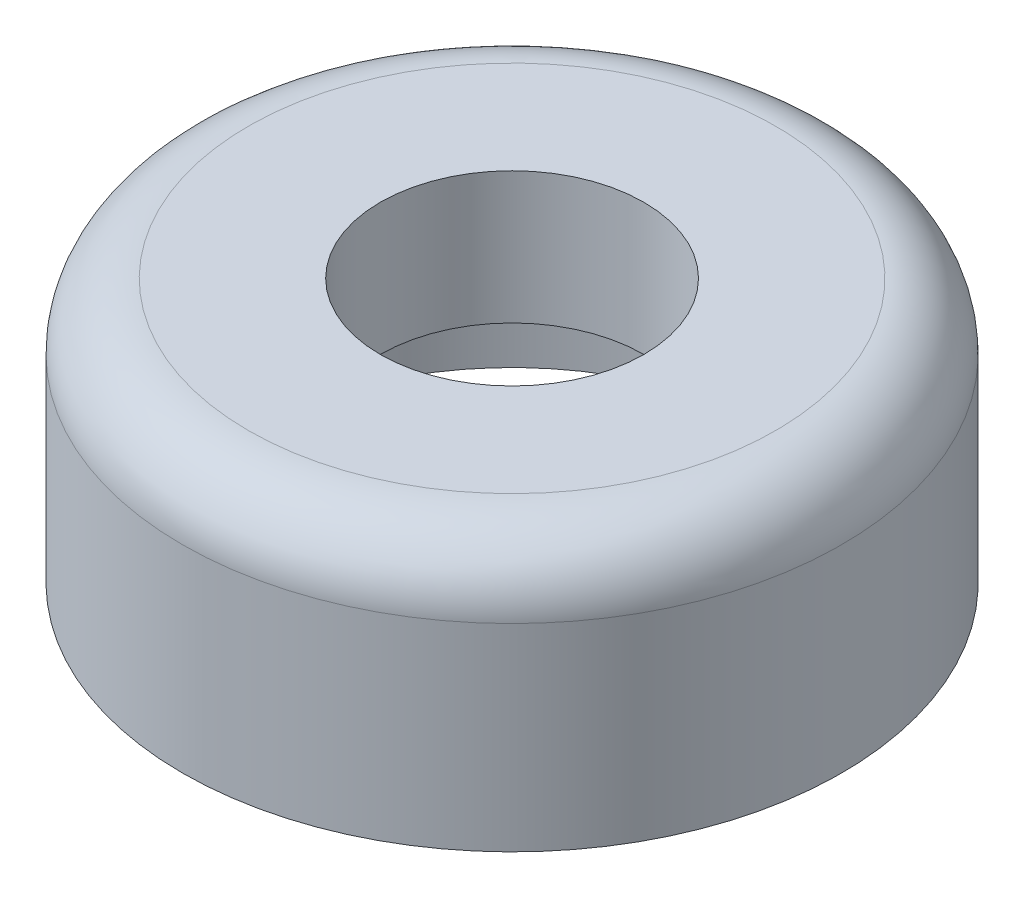
SolidWorks part; units mm, degrees
ref_plane "Plane1" through (0, 0, 0) normal (0, 0, 1) x (1, 0, 0)
ref_plane "Plane2" through (0, 0, 0) normal (0, 1, 0) x (1, 0, 0)
ref_plane "Plane3" through (0, 0, 0) normal (1, 0, 0) x (0, 0, -1)
sketch "Sketch1" plane through (0, 0, 0) normal (0, 0, 1) x (1, 0, 0)
  line L0 (50.8, 101.6) -> (50.8, 50.8)
  line L1 (101.6, 25.4) -> (76.2, 50.8)
  line L2 (101.6, 25.4) -> (101.6, 0)
  line L3 (50.8, 101.6) -> (101.6, 101.6)
  line L4 (127, 76.2) -> (127, 0)
  line L5 (127, 0) -> (101.6, 0)
  line L6 (76.2, 50.8) -> (50.8, 50.8)
  line L7 (0, 127) -> (0, -50.8) construction
  arc A0 (127, 76.2) -> (101.6, 101.6) centre (101.6, 76.2) ccw
  dimension "D1" = 25.4
  dimension "D2" = 50.8
  dimension "D3" = 25.4
  dimension "D4" = 25.4
  dimension "D5" = 101.6
  dimension "D6" = 76.2
  dimension "D7" = 50.8
  dimension "D9" = 50.8
revolve "Base-Revolve" add sketch "Sketch1" angle 360 about L7
